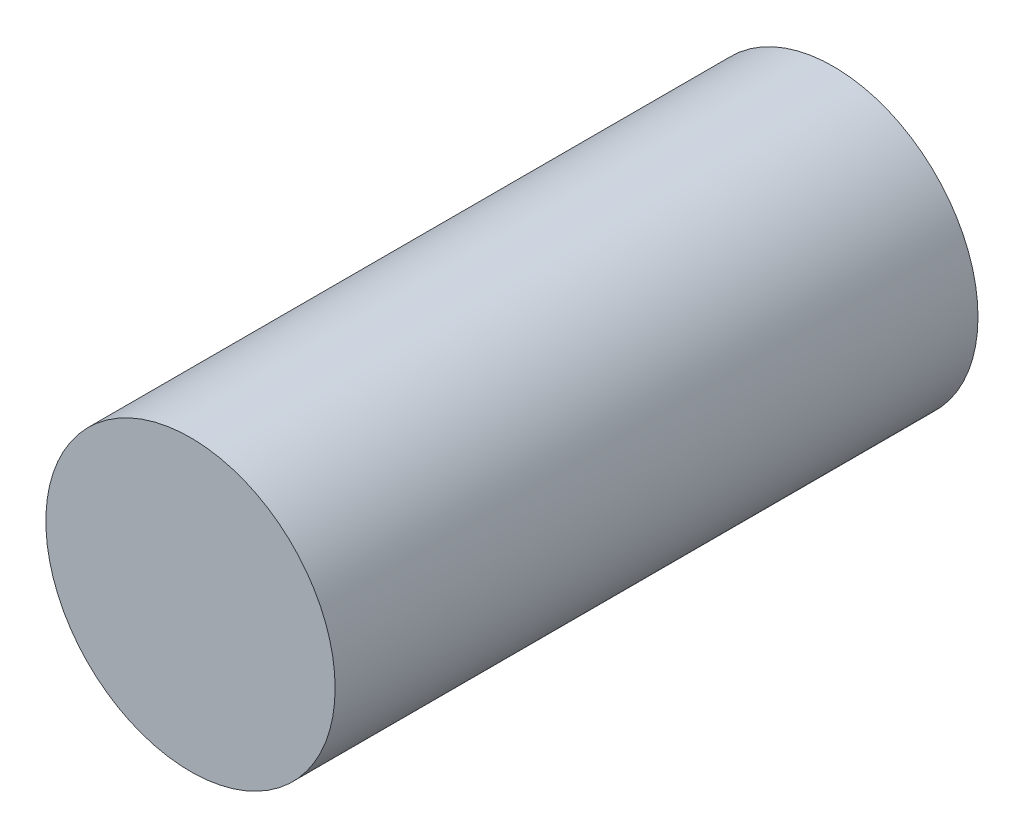
SolidWorks part; units mm, degrees
ref_plane "Front Plane" through (0, 0, 0) normal (0, 0, 1) x (1, 0, 0)
ref_plane "Top Plane" through (0, 0, 0) normal (0, 1, 0) x (1, 0, 0)
ref_plane "Right Plane" through (0, 0, 0) normal (1, 0, 0) x (0, 0, -1)
sketch "Sketch1" plane through (0, 0, 0) normal (0, 0, 1) x (1, 0, 0)
  circle A0 centre (0, 0) radius 4.5
  dimension "D1" = 9
extrude "Boss-Extrude1" add sketch "Sketch1" along normal blind 20
